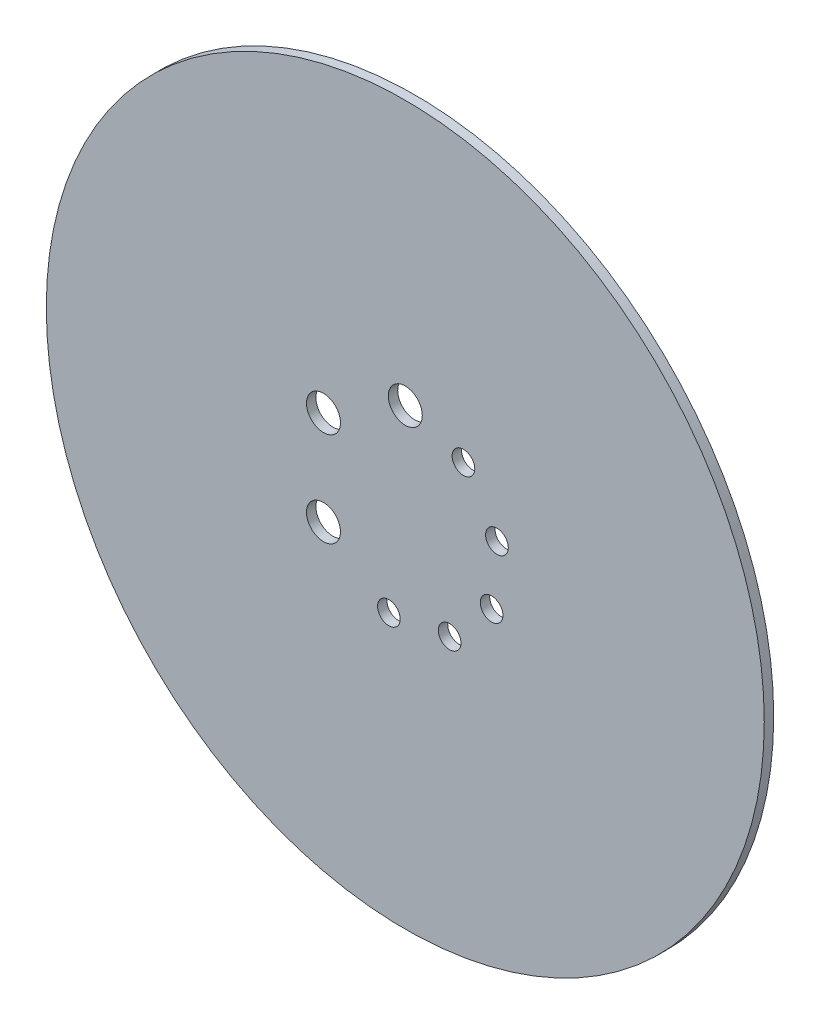
SolidWorks part; units mm, degrees
material "6061 Alloy"
ref_plane "Front Plane" through (0, 0, 0) normal (0, 0, 1) x (1, 0, 0)
ref_plane "Top Plane" through (0, 0, 0) normal (0, 1, 0) x (1, 0, 0)
ref_plane "Right Plane" through (0, 0, 0) normal (1, 0, 0) x (0, 0, -1)
sketch "Sketch1" plane through (0, 0, 0) normal (0, 0, 1) x (1, 0, 0)
  circle A0 centre (0, 0) radius 190
  dimension "D1" = 380
extrude "Boss-Extrude1" add sketch "Sketch1" along normal blind 5
sketch "Sketch2" plane through (0, 0, 0) normal (0, 0, -1) x (-1, 0, 0)
  line L0 (0, 50) -> (0, 0) construction
  line L1 (0, 0) -> (43.3013, -25) construction
  line L2 (0, 0) -> (43.3013, 25) construction
  line L3 (0, 0) -> (-30.7831, 39.4005) construction
  line L4 (0, 0) -> (-48.5148, 12.0961) construction
  line L5 (0, 0) -> (-45.6773, -20.3368) construction
  line L6 (0, 0) -> (-23.4736, -44.1474) construction
  line L7 (0, 0) -> (8.6824, -49.2404) construction
  circle A0 centre (0, 50) radius 9
  circle A1 centre (43.3013, 25) radius 9
  circle A2 centre (43.3013, -25) radius 9
  circle A3 centre (-30.7831, 39.4005) radius 6
  circle A4 centre (-48.5148, 12.0961) radius 6
  circle A5 centre (-45.6773, -20.3368) radius 6
  circle A6 centre (-23.4736, -44.1474) radius 6
  circle A7 centre (8.6824, -49.2404) radius 6
  dimension "D1" = 18
  dimension "D7" = 12
  dimension "D2" = 60
  dimension "D3" = 60
  dimension "D4" = 50
  dimension "D5" = 38
  dimension "D6" = 50
  dimension "D8" = 38
  dimension "D9" = 38
  dimension "D10" = 38
  dimension "D11" = 38
extrude "Cut-Extrude1" cut sketch "Sketch2" against normal blind 10
equation "\"D9@Sketch2\"=\"D5@Sketch2\""
equation "\"D10@Sketch2\"=\"D5@Sketch2\""
equation "\"D8@Sketch2\"=\"D5@Sketch2\""
equation "\"D11@Sketch2\"=\"D5@Sketch2\""
